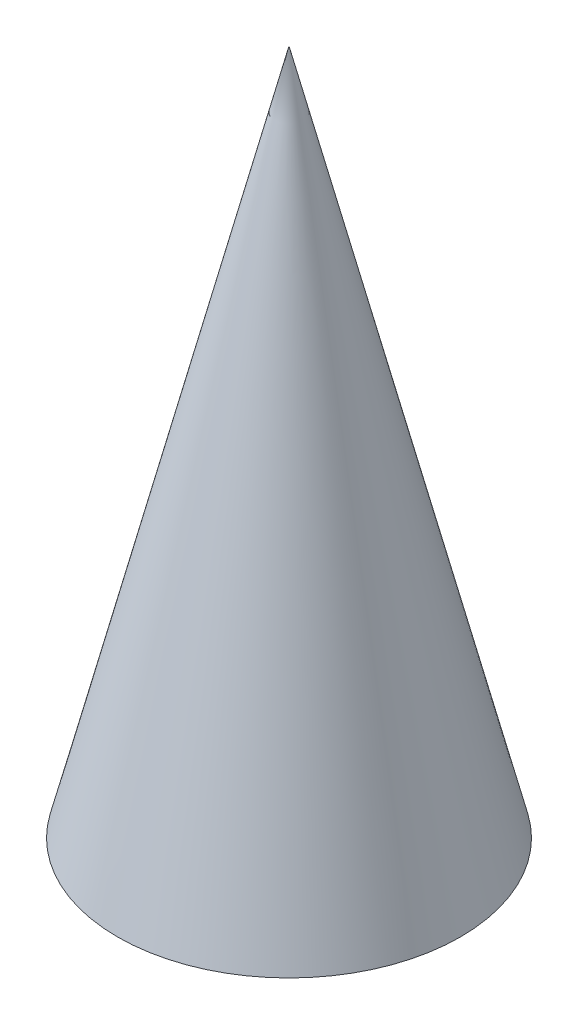
SolidWorks part; units mm, degrees
ref_plane "Front Plane" through (0, 0, 0) normal (0, 0, 1) x (1, 0, 0)
ref_plane "Top Plane" through (0, 0, 0) normal (0, 1, 0) x (1, 0, 0)
ref_plane "Right Plane" through (0, 0, 0) normal (1, 0, 0) x (0, 0, -1)
sketch "Sketch1" plane through (0, 0, 0) normal (0, 0, 1) x (1, 0, 0)
  line L0 (0, 0) -> (10, 0)
  line L1 (10, 0) -> (0, 40)
  line L2 (0, 40) -> (0, 0)
  dimension "D1" = 10
  dimension "D2" = 40
revolve "Revolve1" add sketch "Sketch1" angle 360 about L2
